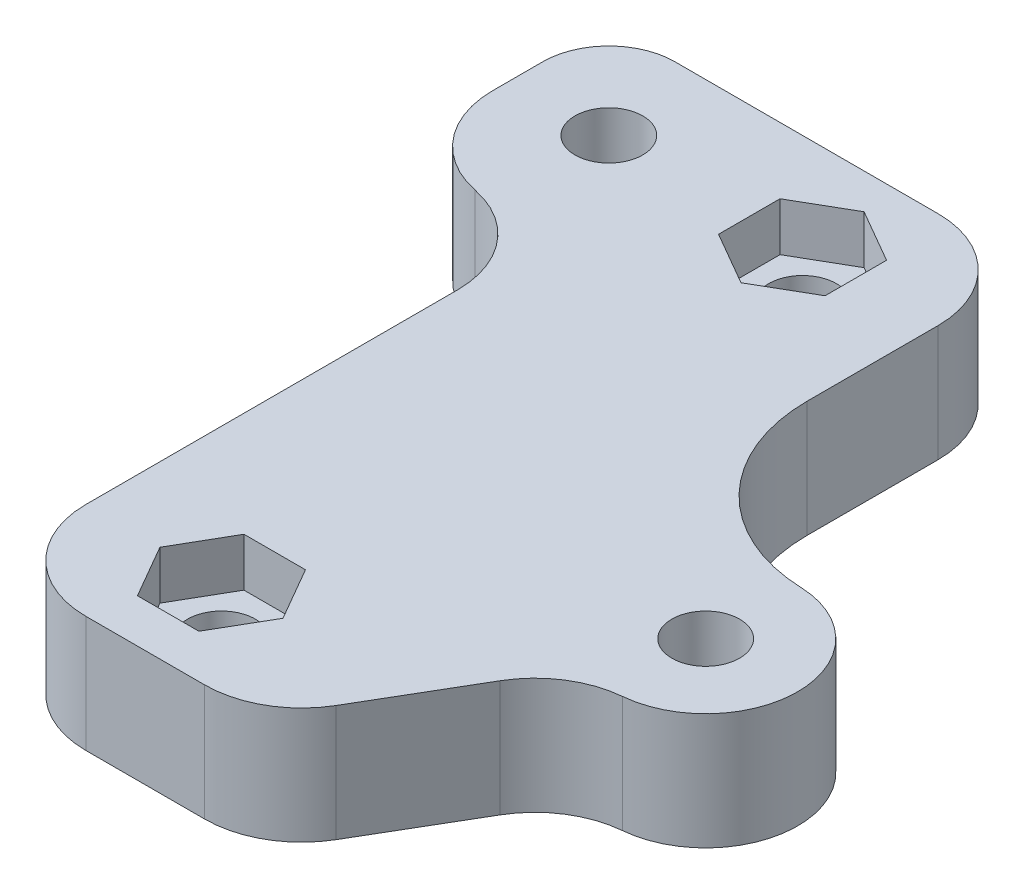
SolidWorks part; units mm, degrees
material "ABS PC"
ref_plane "Front Plane" through (0, 0, 0) normal (0, 0, 1) x (1, 0, 0)
ref_plane "Top Plane" through (0, 0, 0) normal (0, 1, 0) x (1, 0, 0)
ref_plane "Right Plane" through (0, 0, 0) normal (1, 0, 0) x (0, 0, -1)
sketch "Sketch2" plane through (0, 0, 0) normal (0, 1, 0) x (1, 0, 0)
  line L0 (0, 0) -> (35, 0)
  line L1 (0, 0) -> (0, 40)
  line L2 (35, 0) -> (35, 40)
  line L3 (0, 40) -> (35, 40)
  circle A0 centre (5, 35) radius 1.75
  circle A1 centre (30, 15) radius 1.75
  circle A6 centre (15, 35) radius 1.75
  circle A7 centre (15, 5) radius 1.75
  dimension "D3" = 3.5
  dimension "D4" = 25
  dimension "D5" = 20
  dimension "D6" = 5
  dimension "D7" = 5
  dimension "D8" = 35
  dimension "D2" = 40
  dimension "D13" = 10
  dimension "D14" = 5
extrude "Boss-Extrude2" add sketch "Sketch2" along normal blind 6
sketch "Sketch3" plane through (0, 0, 0) normal (0, -1, 0) x (1, 0, 0)
  line L1 (7.75, -36.5877) -> (7.75, -33.4123)
  line L2 (7.75, -33.4123) -> (5, -31.8246)
  line L3 (5, -31.8246) -> (2.25, -33.4123)
  line L4 (2.25, -33.4123) -> (2.25, -36.5877)
  line L5 (2.25, -36.5877) -> (5, -38.1754)
  line L6 (5, -38.1754) -> (7.75, -36.5877)
  line L7 (30, -11.8246) -> (27.25, -13.4123)
  line L8 (27.25, -13.4123) -> (27.25, -16.5877)
  line L9 (27.25, -16.5877) -> (30, -18.1754)
  line L10 (30, -18.1754) -> (32.75, -16.5877)
  line L11 (32.75, -16.5877) -> (32.75, -13.4123)
  line L12 (32.75, -13.4123) -> (30, -11.8246)
  circle A0 centre (5, -35) radius 2.75 construction
  circle A2 centre (30, -15) radius 2.75 construction
  circle A3 centre (5, -35) radius 1.75 construction
  dimension "D1" = 5.5
extrude "Cut-Extrude1" cut sketch "Sketch3" against normal blind 2.5
sketch "Sketch4" plane through (0, 6, 0) normal (0, 1, 0) x (1, 0, 0)
  line L1 (17.75, 36.5877) -> (15, 38.1754)
  line L2 (15, 38.1754) -> (12.25, 36.5877)
  line L3 (12.25, 36.5877) -> (12.25, 33.4123)
  line L4 (12.25, 33.4123) -> (15, 31.8246)
  line L5 (15, 31.8246) -> (17.75, 33.4123)
  line L6 (17.75, 33.4123) -> (17.75, 36.5877)
  line L7 (13.4123, 7.75) -> (11.8246, 5)
  line L8 (11.8246, 5) -> (13.4123, 2.25)
  line L9 (13.4123, 2.25) -> (16.5877, 2.25)
  line L10 (16.5877, 2.25) -> (18.1754, 5)
  line L11 (18.1754, 5) -> (16.5877, 7.75)
  line L12 (16.5877, 7.75) -> (13.4123, 7.75)
  circle A0 centre (15, 35) radius 2.75 construction
  circle A1 centre (15, 5) radius 2.75 construction
  dimension "D1" = 5.5
extrude "Cut-Extrude2" cut sketch "Sketch4" against normal blind 2.5
sketch "Sketch5" plane through (0, 6, 0) normal (0, 1, 0) x (1, 0, 0)
  line L0 (0, 36.5877) -> (0, 40)
  line L1 (0, 40) -> (0, 0) construction
  line L2 (0, 40) -> (3.4123, 40)
  line L3 (35, 40) -> (0, 40) construction
  line L5 (30, 19.75) -> (22, 19.75)
  line L6 (22, 19.75) -> (22, 40)
  line L7 (22, 40) -> (35, 40)
  line L8 (35, 40) -> (35, 0)
  line L9 (35, 0) -> (22, 0)
  line L10 (0, 0) -> (35, 0) construction
  line L11 (30, 10.25) -> (28, 10.25)
  line L12 (28, 10.25) -> (22, 0)
  line L13 (0, 34) -> (0, 0)
  line L14 (0, 0) -> (8, 0)
  line L15 (8, 0) -> (8, 29)
  line L16 (8, 29) -> (5, 29)
  arc A0 (0, 36.5877) -> (3.4123, 40) centre (3.4123, 36.5877) cw
  arc A1 (30, 19.75) -> (30, 10.25) centre (30, 15) cw
  circle A3 centre (15, 5) radius 1.75 construction
  circle A4 centre (5, 35) radius 1.75 construction
  arc A5 (0, 34) -> (5, 29) centre (5, 34) ccw
  circle A6 centre (30, 15) radius 1.75 construction
  dimension "D1" = 4.75
  dimension "D5" = 6
  dimension "D2" = 7
  dimension "D3" = 9.5
  dimension "D4" = 2
  dimension "D6" = 5
  dimension "D7" = 7
extrude "Cut-Extrude3" cut sketch "Sketch5" against normal through all
fillet "Fillet3" radius 5 5 edges at (28, 3, -10.25) (22, 3, 0) (22, 3, -40) (8, 3, -29) (8, 3, 0)
fillet "Fillet4" radius 8.5 1 edges at (22, 3, -19.75)
